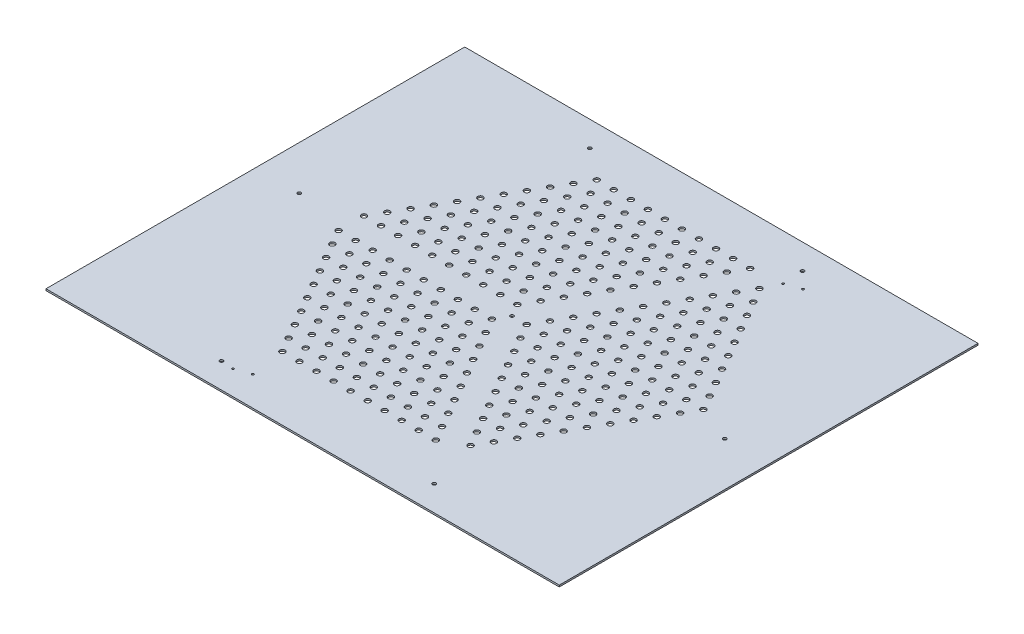
SolidWorks part; units mm, degrees
material "Pine"
ref_plane "Front Plane" through (0, 0, 0) normal (0, 0, 1) x (1, 0, 0)
ref_plane "Top Plane" through (0, 0, 0) normal (0, 1, 0) x (1, 0, 0)
ref_plane "Right Plane" through (0, 0, 0) normal (1, 0, 0) x (0, 0, -1)
sketch "Sketch1" plane through (0, 0, 0) normal (0, 1, 0) x (1, 0, 0)
  line L7 (-482.6, 393.7) -> (482.6, 393.7)
  line L8 (-482.6, 393.7) -> (-482.6, -393.7)
  line L9 (-482.6, -393.7) -> (482.6, -393.7)
  line L10 (482.6, 393.7) -> (482.6, -393.7)
  point P0 (0, 393.7)
  point P2 (-482.6, 0)
  dimension "D1" = 787.4
  dimension "D2" = 965.2
extrude "Base" add sketch "Sketch1" along normal blind 3.175
sketch "Border Sketch" plane through (0, 3.175, 0) normal (0, 1, 0) x (1, 0, 0)
  line L7 (450, 0) -> (225, 389.7114)
  line L8 (225, 389.7114) -> (-225, 389.7114)
  line L9 (-225, 389.7114) -> (-450, 0)
  line L10 (-450, 0) -> (-225, -389.7114)
  line L11 (-225, -389.7114) -> (225, -389.7114)
  line L12 (225, -389.7114) -> (450, 0)
  line L14 (225, 389.7114) -> (0, 0)
  line L15 (0, 0) -> (225, -389.7114)
  line L20 (-450, 0) -> (0, 0)
  line L21 (0, 5.5) -> (-446.8246, 5.5)
  line L22 (0, -5.5) -> (-446.8246, -5.5)
  line L23 (218.6491, 389.7114) -> (-4.7631, 2.75)
  line L24 (4.7631, -2.75) -> (228.1754, 384.2114)
  line L25 (4.7631, 2.75) -> (228.1754, -384.2114)
  line L26 (-4.7631, -2.75) -> (218.6491, -389.7114)
  circle A0 centre (0, 0) radius 450 construction
  circle A1 centre (0, 0) radius 5.5
  dimension "D1" = 5.5
  dimension "D2" = 5.5
  dimension "D3" = 5.5
  dimension "D4" = 5.5
sketch "Sketch3" plane through (0, 3.175, 0) normal (0, 1, 0) x (1, 0, 0)
  circle A1 centre (27.6379, 0.0432) radius 5
  circle A2 centre (43.6579, 27.7907) radius 5
  circle A3 centre (59.6779, 55.5381) radius 5
  circle A4 centre (75.6979, 83.2856) radius 5
  circle A5 centre (91.7179, 111.0331) radius 5
  circle A6 centre (107.7379, 138.7805) radius 5
  circle A7 centre (123.7579, 166.528) radius 5
  circle A8 centre (139.7779, 194.2754) radius 5
  circle A9 centre (155.7979, 222.0229) radius 5
  circle A10 centre (171.8179, 249.7703) radius 5
  circle A11 centre (187.8379, 277.5178) radius 5
  circle A12 centre (59.6779, 0.0432) radius 5
  circle A13 centre (75.6979, 27.7907) radius 5
  circle A14 centre (91.7179, 55.5381) radius 5
  circle A15 centre (107.7379, 83.2856) radius 5
  circle A16 centre (123.7579, 111.0331) radius 5
  circle A17 centre (139.7779, 138.7805) radius 5
  circle A18 centre (155.7979, 166.528) radius 5
  circle A19 centre (171.8179, 194.2754) radius 5
  circle A20 centre (187.8379, 222.0229) radius 5
  circle A21 centre (203.8579, 249.7703) radius 5
  circle A22 centre (75.6979, -27.7042) radius 5
  circle A23 centre (91.7179, 0.0432) radius 5
  circle A24 centre (107.7379, 27.7907) radius 5
  circle A25 centre (123.7579, 55.5381) radius 5
  circle A26 centre (139.7779, 83.2856) radius 5
  circle A27 centre (155.7979, 111.0331) radius 5
  circle A28 centre (171.8179, 138.7805) radius 5
  circle A29 centre (187.8379, 166.528) radius 5
  circle A30 centre (203.8579, 194.2754) radius 5
  circle A31 centre (219.8779, 222.0229) radius 5
  circle A32 centre (91.7179, -55.4517) radius 5
  circle A33 centre (107.7379, -27.7042) radius 5
  circle A34 centre (123.7579, 0.0432) radius 5
  circle A35 centre (139.7779, 27.7907) radius 5
  circle A36 centre (155.7979, 55.5381) radius 5
  circle A37 centre (171.8179, 83.2856) radius 5
  circle A38 centre (187.8379, 111.0331) radius 5
  circle A39 centre (203.8579, 138.7805) radius 5
  circle A40 centre (219.8779, 166.528) radius 5
  circle A41 centre (235.8979, 194.2754) radius 5
  circle A42 centre (107.7379, -83.1991) radius 5
  circle A43 centre (123.7579, -55.4517) radius 5
  circle A44 centre (139.7779, -27.7042) radius 5
  circle A45 centre (155.7979, 0.0432) radius 5
  circle A46 centre (171.8179, 27.7907) radius 5
  circle A47 centre (187.8379, 55.5381) radius 5
  circle A48 centre (203.8579, 83.2856) radius 5
  circle A49 centre (219.8779, 111.0331) radius 5
  circle A50 centre (235.8979, 138.7805) radius 5
  circle A51 centre (251.9179, 166.528) radius 5
  circle A52 centre (123.7579, -110.9466) radius 5
  circle A53 centre (139.7779, -83.1991) radius 5
  circle A54 centre (155.7979, -55.4517) radius 5
  circle A55 centre (171.8179, -27.7042) radius 5
  circle A56 centre (187.8379, 0.0432) radius 5
  circle A57 centre (203.8579, 27.7907) radius 5
  circle A58 centre (219.8779, 55.5381) radius 5
  circle A59 centre (235.8979, 83.2856) radius 5
  circle A60 centre (251.9179, 111.0331) radius 5
  circle A61 centre (267.9379, 138.7805) radius 5
  circle A62 centre (139.7779, -138.694) radius 5
  circle A63 centre (155.7979, -110.9466) radius 5
  circle A64 centre (171.8179, -83.1991) radius 5
  circle A65 centre (187.8379, -55.4517) radius 5
  circle A66 centre (203.8579, -27.7042) radius 5
  circle A67 centre (219.8779, 0.0432) radius 5
  circle A68 centre (235.8979, 27.7907) radius 5
  circle A69 centre (251.9179, 55.5381) radius 5
  circle A70 centre (267.9379, 83.2856) radius 5
  circle A71 centre (283.9579, 111.0331) radius 5
  circle A72 centre (155.7979, -166.4415) radius 5
  circle A73 centre (171.8179, -138.694) radius 5
  circle A74 centre (187.8379, -110.9466) radius 5
  circle A75 centre (203.8579, -83.1991) radius 5
  circle A76 centre (219.8779, -55.4517) radius 5
  circle A77 centre (235.8979, -27.7042) radius 5
  circle A78 centre (251.9179, 0.0432) radius 5
  circle A79 centre (267.9379, 27.7907) radius 5
  circle A80 centre (283.9579, 55.5381) radius 5
  circle A81 centre (299.9779, 83.2856) radius 5
  circle A82 centre (171.8179, -194.1889) radius 5
  circle A83 centre (187.8379, -166.4415) radius 5
  circle A84 centre (203.8579, -138.694) radius 5
  circle A85 centre (219.8779, -110.9466) radius 5
  circle A86 centre (235.8979, -83.1991) radius 5
  circle A87 centre (251.9179, -55.4517) radius 5
  circle A88 centre (267.9379, -27.7042) radius 5
  circle A89 centre (283.9579, 0.0432) radius 5
  circle A90 centre (299.9779, 27.7907) radius 5
  circle A91 centre (315.9979, 55.5381) radius 5
  circle A92 centre (187.8379, -221.9364) radius 5
  circle A93 centre (203.8579, -194.1889) radius 5
  circle A94 centre (219.8779, -166.4415) radius 5
  circle A95 centre (235.8979, -138.694) radius 5
  circle A96 centre (251.9179, -110.9466) radius 5
  circle A97 centre (267.9379, -83.1991) radius 5
  circle A98 centre (283.9579, -55.4517) radius 5
  circle A99 centre (299.9779, -27.7042) radius 5
  circle A100 centre (315.9979, 0.0432) radius 5
  circle A101 centre (332.0179, 27.7907) radius 5
  circle A102 centre (43.6579, -27.7042) radius 5
  circle A103 centre (59.6779, -55.4517) radius 5
  circle A104 centre (75.6979, -83.1991) radius 5
  circle A105 centre (91.7179, -110.9466) radius 5
  circle A106 centre (107.7379, -138.694) radius 5
  circle A107 centre (123.7579, -166.4415) radius 5
  circle A108 centre (139.7779, -194.1889) radius 5
  circle A109 centre (155.7979, -221.9364) radius 5
  circle A110 centre (171.8179, -249.6838) radius 5
  circle A111 centre (-13.8564, -23.9135) radius 5
  circle A112 centre (-45.8964, -23.9135) radius 5
  circle A113 centre (-77.9364, -23.9135) radius 5
  circle A114 centre (-109.9764, -23.9135) radius 5
  circle A115 centre (-142.0164, -23.9135) radius 5
  circle A116 centre (-174.0564, -23.9135) radius 5
  circle A117 centre (-206.0964, -23.9135) radius 5
  circle A118 centre (-238.1364, -23.9135) radius 5
  circle A119 centre (-270.1764, -23.9135) radius 5
  circle A120 centre (-302.2164, -23.9135) radius 5
  circle A121 centre (-29.8764, -51.661) radius 5
  circle A122 centre (-61.9164, -51.661) radius 5
  circle A123 centre (-93.9564, -51.661) radius 5
  circle A124 centre (-125.9964, -51.661) radius 5
  circle A125 centre (-158.0364, -51.661) radius 5
  circle A126 centre (-190.0764, -51.661) radius 5
  circle A127 centre (-222.1164, -51.661) radius 5
  circle A128 centre (-254.1564, -51.661) radius 5
  circle A129 centre (-286.1964, -51.661) radius 5
  circle A130 centre (-13.8564, -79.4084) radius 5
  circle A131 centre (-45.8964, -79.4084) radius 5
  circle A132 centre (-77.9364, -79.4084) radius 5
  circle A133 centre (-109.9764, -79.4084) radius 5
  circle A134 centre (-142.0164, -79.4084) radius 5
  circle A135 centre (-174.0564, -79.4084) radius 5
  circle A136 centre (-206.0964, -79.4084) radius 5
  circle A137 centre (-238.1364, -79.4084) radius 5
  circle A138 centre (-270.1764, -79.4084) radius 5
  circle A139 centre (2.1636, -107.1559) radius 5
  circle A140 centre (-29.8764, -107.1559) radius 5
  circle A141 centre (-61.9164, -107.1559) radius 5
  circle A142 centre (-93.9564, -107.1559) radius 5
  circle A143 centre (-125.9964, -107.1559) radius 5
  circle A144 centre (-158.0364, -107.1559) radius 5
  circle A145 centre (-190.0764, -107.1559) radius 5
  circle A146 centre (-222.1164, -107.1559) radius 5
  circle A147 centre (-254.1564, -107.1559) radius 5
  circle A148 centre (18.1836, -134.9033) radius 5
  circle A149 centre (-13.8564, -134.9033) radius 5
  circle A150 centre (-45.8964, -134.9033) radius 5
  circle A151 centre (-77.9364, -134.9033) radius 5
  circle A152 centre (-109.9764, -134.9033) radius 5
  circle A153 centre (-142.0164, -134.9033) radius 5
  circle A154 centre (-174.0564, -134.9033) radius 5
  circle A155 centre (-206.0964, -134.9033) radius 5
  circle A156 centre (-238.1364, -134.9033) radius 5
  circle A157 centre (34.2036, -162.6508) radius 5
  circle A158 centre (2.1636, -162.6508) radius 5
  circle A159 centre (-29.8764, -162.6508) radius 5
  circle A160 centre (-61.9164, -162.6508) radius 5
  circle A161 centre (-93.9564, -162.6508) radius 5
  circle A162 centre (-125.9964, -162.6508) radius 5
  circle A163 centre (-158.0364, -162.6508) radius 5
  circle A164 centre (-190.0764, -162.6508) radius 5
  circle A165 centre (-222.1164, -162.6508) radius 5
  circle A166 centre (50.2236, -190.3982) radius 5
  circle A167 centre (18.1836, -190.3982) radius 5
  circle A168 centre (-13.8564, -190.3982) radius 5
  circle A169 centre (-45.8964, -190.3982) radius 5
  circle A170 centre (-77.9364, -190.3982) radius 5
  circle A171 centre (-109.9764, -190.3982) radius 5
  circle A172 centre (-142.0164, -190.3982) radius 5
  circle A173 centre (-174.0564, -190.3982) radius 5
  circle A174 centre (-206.0964, -190.3982) radius 5
  circle A175 centre (66.2436, -218.1457) radius 5
  circle A176 centre (34.2036, -218.1457) radius 5
  circle A177 centre (2.1636, -218.1457) radius 5
  circle A178 centre (-29.8764, -218.1457) radius 5
  circle A179 centre (-61.9164, -218.1457) radius 5
  circle A180 centre (-93.9564, -218.1457) radius 5
  circle A181 centre (-125.9964, -218.1457) radius 5
  circle A182 centre (-158.0364, -218.1457) radius 5
  circle A183 centre (-190.0764, -218.1457) radius 5
  circle A184 centre (82.2636, -245.8932) radius 5
  circle A185 centre (50.2236, -245.8932) radius 5
  circle A186 centre (18.1836, -245.8932) radius 5
  circle A187 centre (-13.8564, -245.8932) radius 5
  circle A188 centre (-45.8964, -245.8932) radius 5
  circle A189 centre (-77.9364, -245.8932) radius 5
  circle A190 centre (-109.9764, -245.8932) radius 5
  circle A191 centre (-142.0164, -245.8932) radius 5
  circle A192 centre (-174.0564, -245.8932) radius 5
  circle A193 centre (98.2836, -273.6406) radius 5
  circle A194 centre (66.2436, -273.6406) radius 5
  circle A195 centre (34.2036, -273.6406) radius 5
  circle A196 centre (2.1636, -273.6406) radius 5
  circle A197 centre (-29.8764, -273.6406) radius 5
  circle A198 centre (-61.9164, -273.6406) radius 5
  circle A199 centre (-93.9564, -273.6406) radius 5
  circle A200 centre (-125.9964, -273.6406) radius 5
  circle A201 centre (-158.0364, -273.6406) radius 5
  circle A202 centre (2.1636, -51.661) radius 5
  circle A203 centre (18.1836, -79.4084) radius 5
  circle A204 centre (34.2036, -107.1559) radius 5
  circle A205 centre (50.2236, -134.9033) radius 5
  circle A206 centre (66.2436, -162.6508) radius 5
  circle A207 centre (82.2636, -190.3982) radius 5
  circle A208 centre (98.2836, -218.1457) radius 5
  circle A209 centre (114.3036, -245.8932) radius 5
  circle A210 centre (130.3236, -273.6406) radius 5
  circle A211 centre (-13.8564, 23.9135) radius 5
  circle A212 centre (2.1636, 51.661) radius 5
  circle A213 centre (18.1836, 79.4084) radius 5
  circle A214 centre (34.2036, 107.1559) radius 5
  circle A215 centre (50.2236, 134.9033) radius 5
  circle A216 centre (66.2436, 162.6508) radius 5
  circle A217 centre (82.2636, 190.3982) radius 5
  circle A218 centre (98.2836, 218.1457) radius 5
  circle A219 centre (114.3036, 245.8932) radius 5
  circle A220 centre (130.3236, 273.6406) radius 5
  circle A221 centre (146.3436, 301.3881) radius 5
  circle A222 centre (-29.8764, 51.661) radius 5
  circle A223 centre (-13.8564, 79.4084) radius 5
  circle A224 centre (2.1636, 107.1559) radius 5
  circle A225 centre (18.1836, 134.9033) radius 5
  circle A226 centre (34.2036, 162.6508) radius 5
  circle A227 centre (50.2236, 190.3982) radius 5
  circle A228 centre (66.2436, 218.1457) radius 5
  circle A229 centre (82.2636, 245.8932) radius 5
  circle A230 centre (98.2836, 273.6406) radius 5
  circle A231 centre (114.3036, 301.3881) radius 5
  circle A232 centre (-61.9164, 51.661) radius 5
  circle A233 centre (-45.8964, 79.4084) radius 5
  circle A234 centre (-29.8764, 107.1559) radius 5
  circle A235 centre (-13.8564, 134.9033) radius 5
  circle A236 centre (2.1636, 162.6508) radius 5
  circle A237 centre (18.1836, 190.3982) radius 5
  circle A238 centre (34.2036, 218.1457) radius 5
  circle A239 centre (50.2236, 245.8932) radius 5
  circle A240 centre (66.2436, 273.6406) radius 5
  circle A241 centre (82.2636, 301.3881) radius 5
  circle A242 centre (-93.9564, 51.661) radius 5
  circle A243 centre (-77.9364, 79.4084) radius 5
  circle A244 centre (-61.9164, 107.1559) radius 5
  circle A245 centre (-45.8964, 134.9033) radius 5
  circle A246 centre (-29.8764, 162.6508) radius 5
  circle A247 centre (-13.8564, 190.3982) radius 5
  circle A248 centre (2.1636, 218.1457) radius 5
  circle A249 centre (18.1836, 245.8932) radius 5
  circle A250 centre (34.2036, 273.6406) radius 5
  circle A251 centre (50.2236, 301.3881) radius 5
  circle A252 centre (-125.9964, 51.661) radius 5
  circle A253 centre (-109.9764, 79.4084) radius 5
  circle A254 centre (-93.9564, 107.1559) radius 5
  circle A255 centre (-77.9364, 134.9033) radius 5
  circle A256 centre (-61.9164, 162.6508) radius 5
  circle A257 centre (-45.8964, 190.3982) radius 5
  circle A258 centre (-29.8764, 218.1457) radius 5
  circle A259 centre (-13.8564, 245.8932) radius 5
  circle A260 centre (2.1636, 273.6406) radius 5
  circle A261 centre (18.1836, 301.3881) radius 5
  circle A262 centre (-158.0364, 51.661) radius 5
  circle A263 centre (-142.0164, 79.4084) radius 5
  circle A264 centre (-125.9964, 107.1559) radius 5
  circle A265 centre (-109.9764, 134.9033) radius 5
  circle A266 centre (-93.9564, 162.6508) radius 5
  circle A267 centre (-77.9364, 190.3982) radius 5
  circle A268 centre (-61.9164, 218.1457) radius 5
  circle A269 centre (-45.8964, 245.8932) radius 5
  circle A270 centre (-29.8764, 273.6406) radius 5
  circle A271 centre (-13.8564, 301.3881) radius 5
  circle A272 centre (-190.0764, 51.661) radius 5
  circle A273 centre (-174.0564, 79.4084) radius 5
  circle A274 centre (-158.0364, 107.1559) radius 5
  circle A275 centre (-142.0164, 134.9033) radius 5
  circle A276 centre (-125.9964, 162.6508) radius 5
  circle A277 centre (-109.9764, 190.3982) radius 5
  circle A278 centre (-93.9564, 218.1457) radius 5
  circle A279 centre (-77.9364, 245.8932) radius 5
  circle A280 centre (-61.9164, 273.6406) radius 5
  circle A281 centre (-45.8964, 301.3881) radius 5
  circle A282 centre (-222.1164, 51.661) radius 5
  circle A283 centre (-206.0964, 79.4084) radius 5
  circle A284 centre (-190.0764, 107.1559) radius 5
  circle A285 centre (-174.0564, 134.9033) radius 5
  circle A286 centre (-158.0364, 162.6508) radius 5
  circle A287 centre (-142.0164, 190.3982) radius 5
  circle A288 centre (-125.9964, 218.1457) radius 5
  circle A289 centre (-109.9764, 245.8932) radius 5
  circle A290 centre (-93.9564, 273.6406) radius 5
  circle A291 centre (-77.9364, 301.3881) radius 5
  circle A292 centre (-254.1564, 51.661) radius 5
  circle A293 centre (-238.1364, 79.4084) radius 5
  circle A294 centre (-222.1164, 107.1559) radius 5
  circle A295 centre (-206.0964, 134.9033) radius 5
  circle A296 centre (-190.0764, 162.6508) radius 5
  circle A297 centre (-174.0564, 190.3982) radius 5
  circle A298 centre (-158.0364, 218.1457) radius 5
  circle A299 centre (-142.0164, 245.8932) radius 5
  circle A300 centre (-125.9964, 273.6406) radius 5
  circle A301 centre (-109.9764, 301.3881) radius 5
  circle A302 centre (-286.1964, 51.661) radius 5
  circle A303 centre (-270.1764, 79.4084) radius 5
  circle A304 centre (-254.1564, 107.1559) radius 5
  circle A305 centre (-238.1364, 134.9033) radius 5
  circle A306 centre (-222.1164, 162.6508) radius 5
  circle A307 centre (-206.0964, 190.3982) radius 5
  circle A308 centre (-190.0764, 218.1457) radius 5
  circle A309 centre (-174.0564, 245.8932) radius 5
  circle A310 centre (-158.0364, 273.6406) radius 5
  circle A311 centre (-142.0164, 301.3881) radius 5
  circle A312 centre (-45.8964, 23.9135) radius 5
  circle A313 centre (-77.9364, 23.9135) radius 5
  circle A314 centre (-109.9764, 23.9135) radius 5
  circle A315 centre (-142.0164, 23.9135) radius 5
  circle A316 centre (-174.0564, 23.9135) radius 5
  circle A317 centre (-206.0964, 23.9135) radius 5
  circle A318 centre (-238.1364, 23.9135) radius 5
  circle A319 centre (-270.1764, 23.9135) radius 5
  circle A320 centre (-302.2164, 23.9135) radius 5
  dimension "D1" = 11
  dimension "D3" = 10
  dimension "D5" = 11
  dimension "D2" = 10
  dimension "D4" = 10
  dimension "D6" = 10
extrude "Cut-Extrude1" cut sketch "Sketch3" against normal up to next (3.175 mm away)
hole_wizard "Ø6.5 (6.5) Diameter Hole1" positions "Sketch4" profile "Sketch5" hole size "Ø6.5" standard "ANSI Metric" end condition through all
sketch "Sketch4" plane through (0, -4.7625, 0) normal (0, -1, 0) x (-0.5, 0, 0.866)
  point P0 (0, 0)
  point P3 (-400, 0)
  point P11 (-200, 346.4102)
  point P12 (200, 346.4102)
  point P13 (400, 0)
  point P14 (200, -346.4102)
  point P15 (-200, -346.4102)
  point P16 (0, 0)
sketch "Sketch5" plane through (0, -4.7625, 0) normal (1, 0, 0) x (0, 0, -1)
  line L0 (0, 0) -> (0, 7.9375)
  line L1 (0, 7.9375) -> (3.25, 7.9375)
  line L2 (3.25, 7.9375) -> (3.25, 0)
  line L3 (3.25, 0) -> (0, 0)
  line L4 (0, -6.35) -> (0, 107.95) construction
  dimension "Thru Hole Dia." = 6.5
  dimension "Thru Hole Depth" = 7.9375
hole_wizard "Ø4.0 (4) Diameter Hole1" positions "Sketch6" profile "Sketch7" hole size "Ø4.0" standard "ANSI Metric"
sketch "Sketch6" plane through (0, 9.525, 0) normal (0, 1, 0) x (0.5, 0, -0.866)
  point P0 (-389.7627, -21.2724)
  point P3 (-367.5377, -40.3224)
  point P6 (367.5377, -21.2724)
  point P9 (389.7627, -40.3224)
sketch "Sketch7" plane through (-176.4589, 9.525, 348.1806) normal (1, 0, 0) x (0, 0, 1)
  line L0 (0, 0) -> (0, 9.525)
  line L1 (0, 9.525) -> (2, 9.525)
  line L2 (2, 9.525) -> (2, 0)
  line L3 (2, 0) -> (0, 0)
  line L4 (0, -6.35) -> (0, 107.95) construction
  dimension "Thru Hole Dia." = 4
  dimension "Thru Hole Depth" = 9.525
sketch "Sketch8" plane through (0, 3.175, 0) normal (0, 1, 0) x (1, 0, 0)
  line L1 (433.0127, 0) -> (216.5064, 375)
  line L2 (216.5064, 375) -> (-216.5064, 375)
  line L3 (-216.5064, 375) -> (-433.0127, 0)
  line L4 (-433.0127, 0) -> (-216.5064, -375)
  line L5 (-216.5064, -375) -> (216.5064, -375)
  line L6 (216.5064, -375) -> (433.0127, 0)
